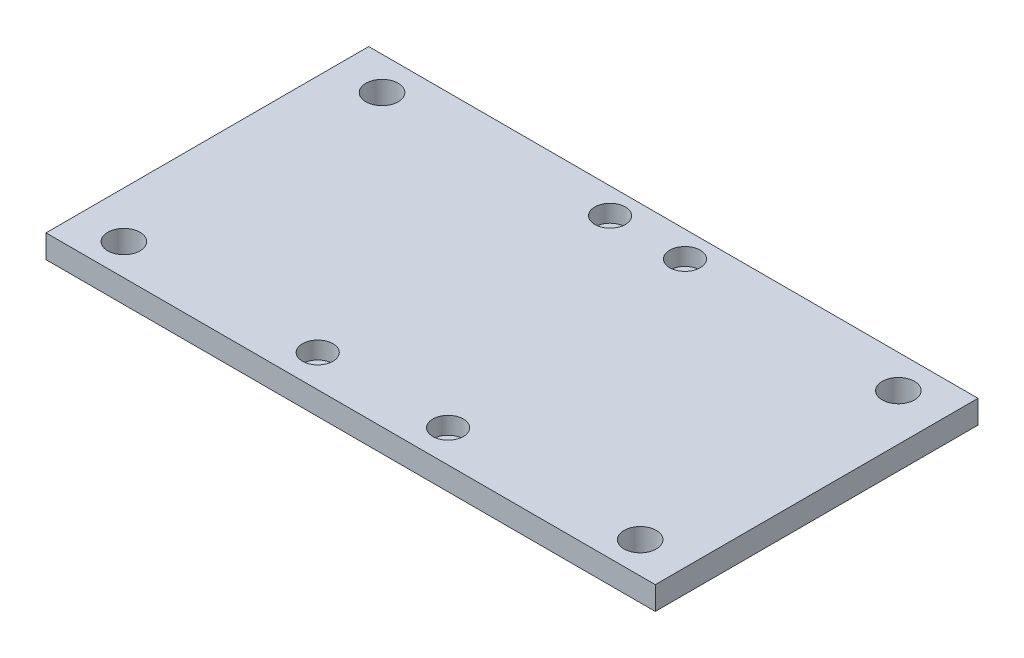
SolidWorks part; units mm, degrees
ref_plane "Front Plane" through (0, 0, 0) normal (0, 0, 1) x (1, 0, 0)
ref_plane "Top Plane" through (0, 0, 0) normal (0, 1, 0) x (1, 0, 0)
ref_plane "Right Plane" through (0, 0, 0) normal (1, 0, 0) x (0, 0, -1)
sketch "Sketch1" plane through (0, 0, 0) normal (0, 1, 0) x (1, 0, 0)
  line L1 (59.944, 31.75) -> (-59.944, 31.75)
  line L2 (59.944, 31.75) -> (59.944, -31.75)
  line L3 (59.944, -31.75) -> (-59.944, -31.75)
  line L4 (-59.944, 31.75) -> (-59.944, -31.75)
  line L5 (59.944, 31.75) -> (-59.944, -31.75) construction
  line L6 (59.944, -31.75) -> (-59.944, 31.75) construction
  point P0 (0, 0)
  dimension "D1" = 119.888
  dimension "D2" = 63.5
extrude "Boss-Extrude1" add sketch "Sketch1" along normal blind 4.572
hole_wizard "CBORE for M3 Hexagon socket head cap screws1" positions "Sketch2" profile "Sketch3" counterbore size "M3" standard "GB" end condition through all
sketch "Sketch2" plane through (0, 4.572, 0) normal (0, 1, 0) x (1, 0, 0)
  line L0 (-7.366, 26.67) -> (7.366, 26.67) construction
  line L2 (-12.827, -25.4) -> (12.827, -25.4) construction
  line L4 (0, 26.67) -> (0, -25.4) construction
  line L6 (59.944, 31.75) -> (-59.944, 31.75) construction
  point P0 (7.366, 26.67)
  point P2 (12.827, -25.4)
  point P4 (-12.827, -25.4)
  point P6 (-7.366, 26.67)
  dimension "D1" = 25.654
  dimension "D2" = 14.732
  dimension "3.05" = 52.07
  dimension "D4" = 5.08
sketch "Sketch3" plane through (7.366, 4.572, -26.67) normal (1, 0, 0) x (0, 0, 1)
  line L0 (0, 0) -> (0, 4.572)
  line L1 (0, 4.572) -> (1.7, 4.572)
  line L3 (1.7, 4.572) -> (1.7, 3.4)
  line L4 (1.7, 3.4) -> (3, 3.4)
  line L5 (3, 3.4) -> (3, 0)
  line L7 (3, 0) -> (0, 0)
  line L11 (0, -6.35) -> (0, 107.95) construction
  dimension "Thru Hole Dia." = 3.4
  dimension "Thru Hole Depth" = 4.572
  dimension "C'Bore Dia." = 6
  dimension "C'Bore Depth" = 3.4
sketch "Sketch5" plane through (0, 4.572, 0) normal (0, 1, 0) x (1, 0, 0)
  circle A0 centre (50.8, 25.2257) radius 3.175
  circle A1 centre (50.8, -25.5743) radius 3.175
  circle A2 centre (-50.8, 25.2257) radius 3.175
  circle A3 centre (-50.8, -25.5743) radius 3.175
  dimension "D1" = 6.35
  dimension "D2" = 6.35
  dimension "D3" = 6.35
  dimension "D4" = 6.35
  dimension "D5" = 50.8
  dimension "D6" = 50.8
  dimension "D7" = 50.8
extrude "Cut-Extrude1" cut sketch "Sketch5" against normal through all
